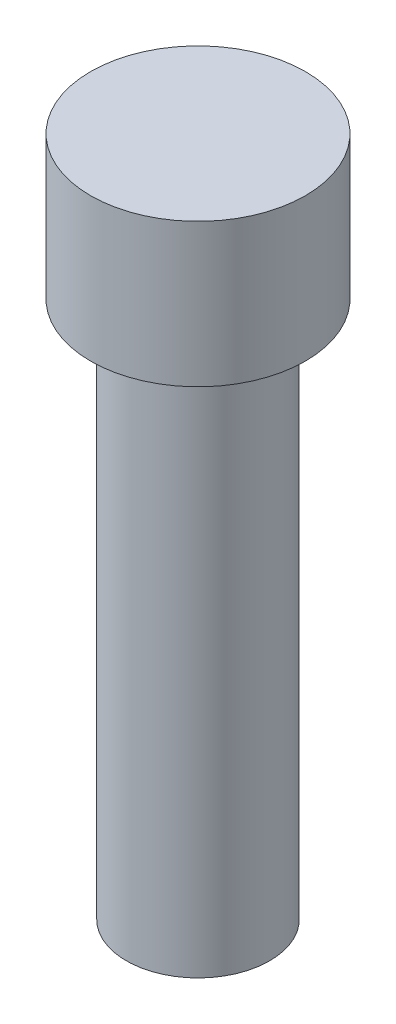
SolidWorks part; units mm, degrees
ref_plane "Front Plane" through (0, 0, 0) normal (0, 0, 1) x (1, 0, 0)
ref_plane "Top Plane" through (0, 0, 0) normal (0, 1, 0) x (1, 0, 0)
ref_plane "Right Plane" through (0, 0, 0) normal (1, 0, 0) x (0, 0, -1)
sketch "Sketch1" plane through (0, 0, 0) normal (0, 0, 1) x (1, 0, 0)
  line L0 (0, 0) -> (0, 45.384) construction
  line L1 (0, 0) -> (-2, 0)
  line L2 (-2, 0) -> (-2, 15)
  line L3 (-2, 15) -> (-3, 15)
  line L4 (-3, 15) -> (-3, 19)
  line L5 (-3, 19) -> (0, 19)
  line L6 (0, 19) -> (0, 0)
  dimension "D1" = 2
  dimension "D2" = 15
  dimension "D3" = 3
  dimension "D4" = 4
revolve "Revolve1" add sketch "Sketch1" angle 360 about L0
